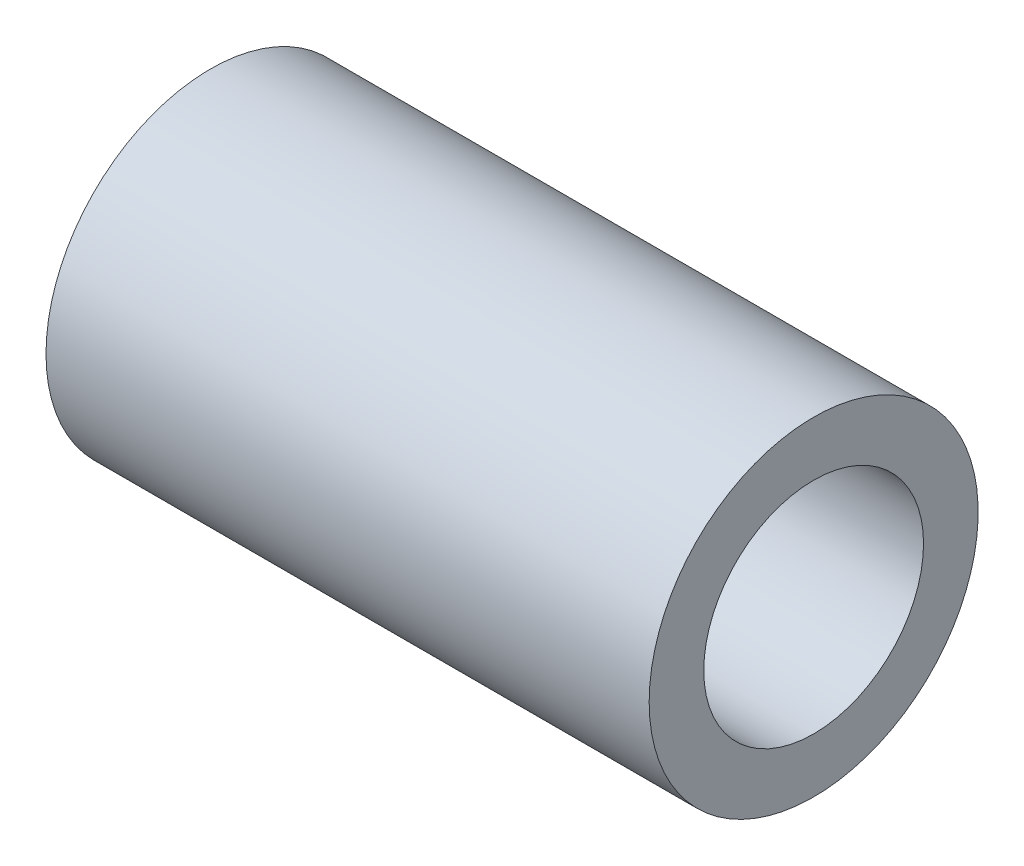
SolidWorks part; units mm, degrees
ref_plane "Front" through (0, 0, 0) normal (0, 0, 1) x (1, 0, 0)
ref_plane "Top" through (0, 0, 0) normal (0, 1, 0) x (1, 0, 0)
ref_plane "Right" through (0, 0, 0) normal (1, 0, 0) x (0, 0, -1)
sketch "Sketch1" plane through (0, 0, 0) normal (0, 0, 1) x (1, 0, 0)
  line L0 (0, 0) -> (66.4064, 0) construction
  line L2 (0, 9.525) -> (34.925, 9.525)
  line L3 (0, 9.525) -> (0, 6.3627)
  line L4 (0, 6.3627) -> (34.925, 6.3627)
  line L5 (34.925, 9.525) -> (34.925, 6.3627)
  dimension "D1" = 12.7254
  dimension "D2" = 19.05
  dimension "D3" = 34.925
revolve "Revolve1" add sketch "Sketch1" angle 360 about L0
